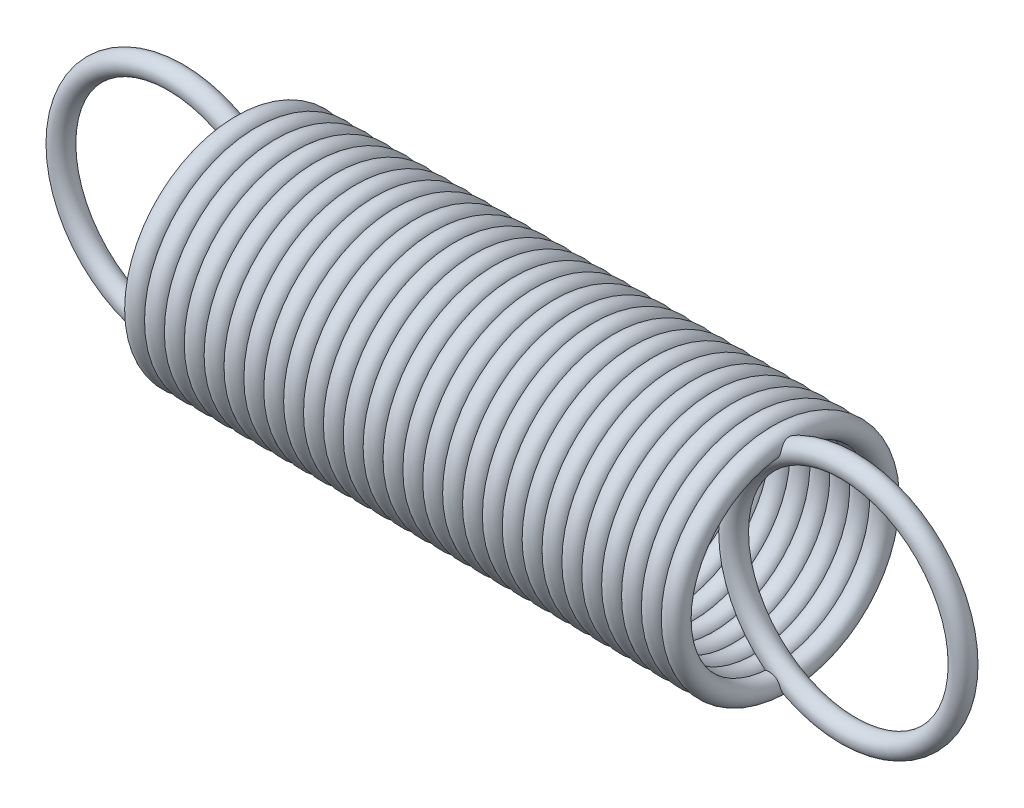
SolidWorks part; units mm, degrees
ref_plane "Front Plane" through (0, 0, 0) normal (0, 0, 1) x (1, 0, 0)
ref_plane "Top Plane" through (0, 0, 0) normal (0, 1, 0) x (1, 0, 0)
ref_plane "Right Plane" through (0, 0, 0) normal (1, 0, 0) x (0, 0, -1)
sketch "Sketch4" plane through (0, 0, 0) normal (0, 1, 0) x (1, 0, 0)
  line L0 (-3.1477, 0) -> (5.0964, 0) construction
  circle A0 centre (0, 2.8829) radius 0.2921
  point P5 (0, 3.175)
  dimension "D1" = 0.5842
  dimension "D2" = 3.175
revolve "Revolve2" add sketch "Sketch4" angle 360 about L0
sketch "Sketch5" plane through (0, 0, 0) normal (0, 1, 0) x (1, 0, 0)
  line L0 (0, 0) -> (5.2074, 0) construction
pattern_linear "LPattern3" count 28 spacing 0.55 along (1, 0, 0) of bodies 103
sketch "Sketch2" plane through (0, 0, 0) normal (0, 1, 0) x (1, 0, 0)
  line L0 (-1.8838, -1.3938) -> (-1.8838, 2.6032) construction
  line L2 (16.7318, -0.2826) -> (16.7318, 2.5255) construction
  point P2 (-0.2963, 0)
  point P3 (15.1443, 0)
  dimension "D1" = 1.5875
  dimension "D2" = 1.5875
sketch "Sketch3" plane through (0, 0, 0) normal (0, 1, 0) x (1, 0, 0)
  line L0 (-1.8838, -1.3938) -> (-1.8838, 2.6032) construction
  circle A0 centre (-5.0588, 0) radius 0.2921
  dimension "D1" = 0.5842
  dimension "D2" = 3.175
revolve "Revolve1" add sketch "Sketch3" angle 360 about L0
sketch "Sketch7" plane through (0, 0, 0) normal (0, 1, 0) x (1, 0, 0)
  line L0 (16.7318, -0.2826) -> (16.7318, 2.5255) construction
  circle A0 centre (19.9068, 0) radius 0.2921
  dimension "D1" = 0.5842
  dimension "D2" = 3.175
revolve "Revolve3" add sketch "Sketch7" angle 360 about L2
sketch "Sketch8" plane through (0, 0, 0) normal (0, 0, 1) x (1, 0, 0)
  circle A0 centre (-1.8838, 0) radius 3.4671 construction
  circle A2 centre (16.7318, 0) radius 3.4671 construction
  point P0 (-5.3509, 0)
  point P4 (20.1989, 0)
